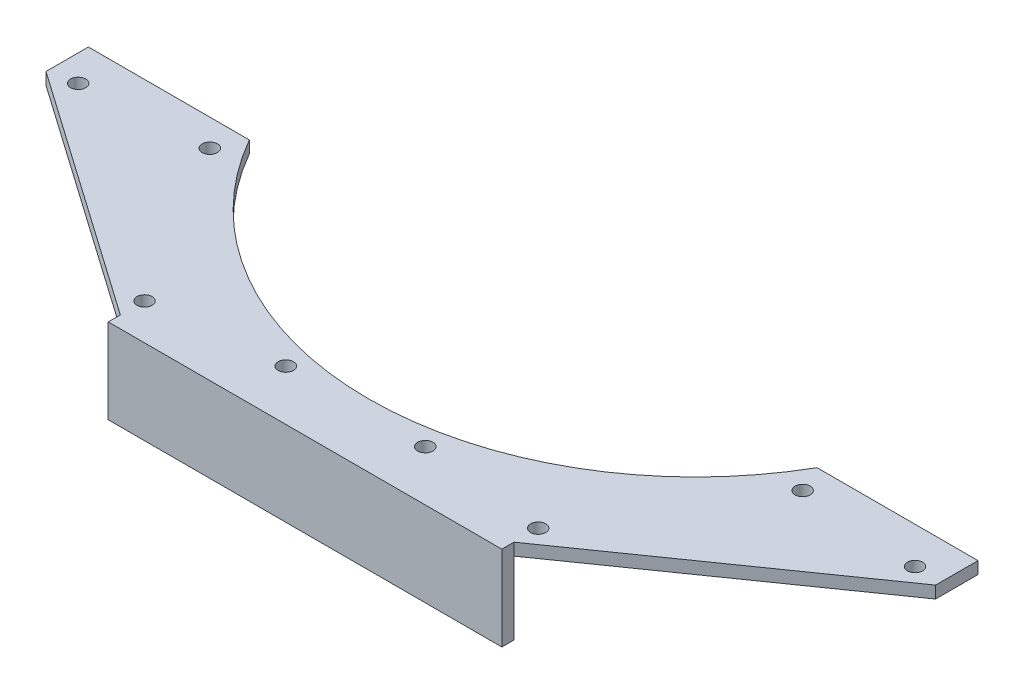
SolidWorks part; units mm, degrees
ref_plane "Front Plane" through (0, 0, 0) normal (0, 0, 1) x (1, 0, 0)
ref_plane "Top Plane" through (0, 0, 0) normal (0, 1, 0) x (1, 0, 0)
ref_plane "Right Plane" through (0, 0, 0) normal (1, 0, 0) x (0, 0, -1)
sketch "Sketch1" plane through (0, 10.3802, 0) normal (0, 1, 0) x (1, 0, 0)
  line L0 (-79.4957, -109.0498) -> (-79.4957, -79.6868) construction
  line L1 (-81.3839, -109.0498) -> (-77.6074, -109.0498) construction
  line L2 (-38.2207, -111.7498) -> (-120.7707, -111.7498)
  line L3 (-86.5154, -111.7498) -> (-72.476, -111.7498) construction
  line L4 (-120.7707, -111.7498) -> (-172.7868, -75.3277)
  line L5 (-172.7868, -75.3277) -> (-172.7868, -66.4377)
  line L6 (-172.7868, -66.4377) -> (-139.0275, -66.4377)
  line L7 (-38.2207, -111.7498) -> (13.7955, -75.3277)
  line L8 (13.7955, -75.3277) -> (13.7955, -66.4377)
  line L12 (-19.9639, -66.4377) -> (13.7955, -66.4377)
  line L13 (-167.2565, -74.1201) -> (-120.7707, -106.6698) construction
  circle A0 centre (-17.3271, -72.0941) radius 1.6 construction
  circle A1 centre (-141.6643, -72.0941) radius 1.6 construction
  circle A2 centre (-94.1274, -103.6998) radius 1.6 construction
  circle A3 centre (-64.8639, -103.6998) radius 1.6 construction
  circle A4 centre (-17.3271, -72.0941) radius 1.6
  circle A5 centre (-141.6643, -72.0941) radius 1.6
  circle A6 centre (-94.1274, -103.6998) radius 1.6
  circle A7 centre (-64.8639, -103.6998) radius 1.6
  arc A8 (-139.0275, -66.4377) -> (-19.9639, -66.4377) centre (-79.4957, -32.3909) ccw
  circle A9 centre (-120.7707, -106.6698) radius 1.5875
  circle A10 centre (-167.2565, -74.1201) radius 1.5875
  circle A11 centre (8.2651, -74.1201) radius 1.5875
  circle A12 centre (-38.2207, -106.6698) radius 1.5875
  point P25 (-79.4957, -97.7798)
  point P29 (-79.4957, -111.7498)
  point P31 (-79.4957, -66.9387)
  dimension "D5" = 68.58
  dimension "D6" = 3.175
  dimension "D7" = 5.08
  dimension "D8" = 3.175
  dimension "D1" = 82.55
  dimension "D2" = 63.5
  dimension "D3" = 145
  dimension "D4" = 8.89
  dimension "D9" = 56.7487
extrude "Boss-Extrude1" add sketch "Sketch1" along normal blind 2.54
sketch "Sketch2" plane through (0, 0, 111.7498) normal (0, 0, 1) x (1, 0, 0)
  line L0 (-120.7707, 12.9202) -> (-38.2207, 12.9202) construction
  line L1 (-120.7707, 12.9202) -> (-38.2207, 12.9202)
  line L2 (-120.7707, 12.9202) -> (-120.7707, -4.8598)
  line L3 (-38.2207, 12.9202) -> (-38.2207, -4.8598)
  line L4 (-120.7707, -4.8598) -> (-38.2207, -4.8598)
  dimension "D1" = 17.78
extrude "Boss-Extrude2" add sketch "Sketch2" along normal blind 2.54
